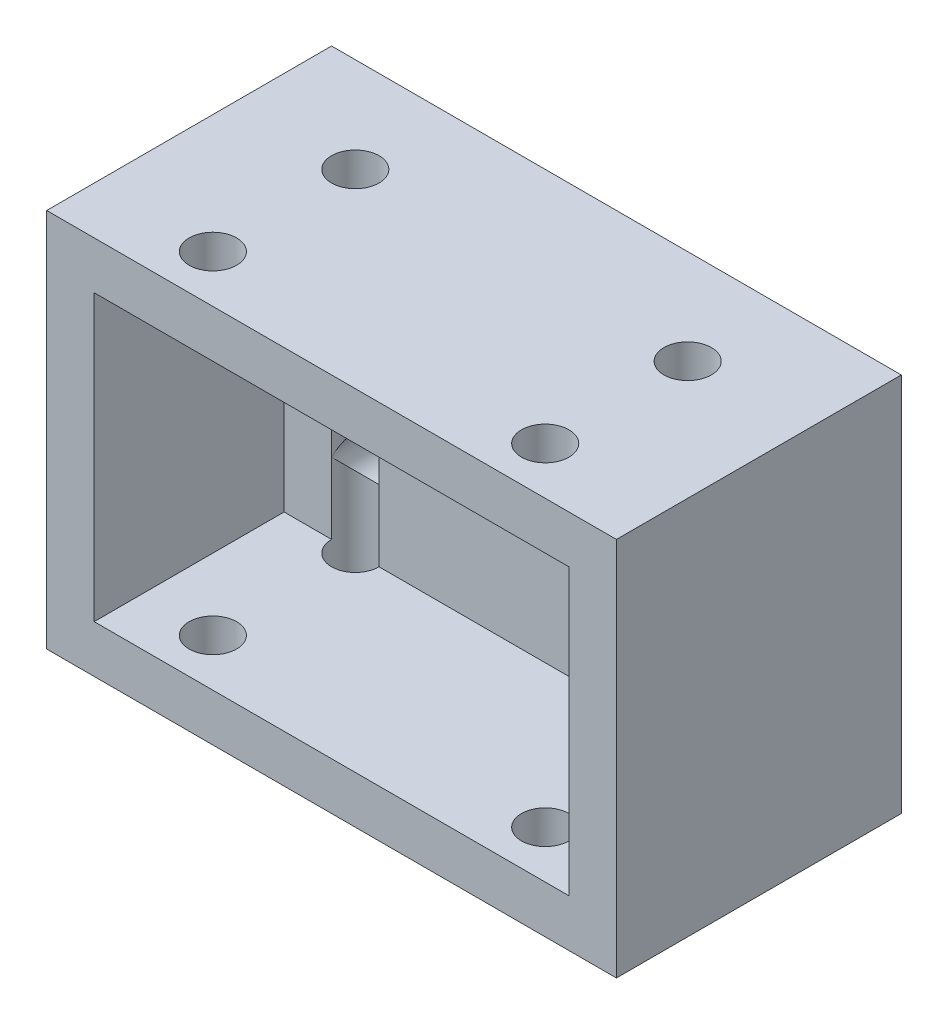
SolidWorks part; units mm, degrees
material "5052-H32"
ref_plane "Front Plane" through (0, 0, 0) normal (0, 0, 1) x (1, 0, 0)
ref_plane "Top Plane" through (0, 0, 0) normal (0, 1, 0) x (1, 0, 0)
ref_plane "Right Plane" through (0, 0, 0) normal (1, 0, 0) x (0, 0, -1)
sketch "Sketch1" plane through (0, 0, 0) normal (0, 0, 1) x (1, 0, 0)
  line L1 (-30, 20) -> (30, 20)
  line L2 (-30, 20) -> (-30, -20)
  line L3 (-30, -20) -> (30, -20)
  line L4 (30, 20) -> (30, -20)
  line L5 (-30, 20) -> (30, -20) construction
  line L6 (-30, -20) -> (30, 20) construction
  circle A0 centre (-17.5, 7.5) radius 2.5
  circle A1 centre (17.5, 7.5) radius 2.5
  circle A2 centre (-17.5, -7.5) radius 2.5
  circle A3 centre (17.5, -7.5) radius 2.5
  point P0 (0, 0)
  dimension "D3" = 5
  dimension "D4" = 5
  dimension "D5" = 5
  dimension "D6" = 5
  dimension "D1" = 60
  dimension "D2" = 40
  dimension "D7" = 12.5
  dimension "D8" = 12.5
  dimension "D9" = 12.5
  dimension "D10" = 12.5
  dimension "D11" = 15
  dimension "D12" = 12.5
  dimension "D13" = 12.5
  dimension "D14" = 15
extrude "Boss-Extrude3" add sketch "Sketch1" along normal blind 30
sketch "Sketch4" plane through (0, 0, 30) normal (0, 0, 1) x (1, 0, 0)
  line L1 (-25, 15) -> (25, 15)
  line L2 (-25, 15) -> (-25, -15)
  line L3 (-25, -15) -> (25, -15)
  line L4 (25, 15) -> (25, -15)
  line L5 (-25, 15) -> (25, -15) construction
  line L6 (-25, -15) -> (25, 15) construction
  point P0 (0, 0)
  dimension "D1" = 50
  dimension "D2" = 30
extrude "Cut-Extrude1" cut sketch "Sketch4" against normal blind 20
sketch "Sketch5" plane through (0, 20, 0) normal (0, 1, 0) x (1, 0, 0)
  line L0 (30, 0) -> (-30, 0) construction
  line L1 (-30, -30) -> (-30, 0) construction
  circle A0 centre (-17.5, -10) radius 2.5
  circle A1 centre (17.5, -10) radius 2.5
  circle A2 centre (17.5, -25) radius 2.5
  circle A3 centre (-17.5, -25) radius 2.5
  point P8 (0, 0)
  point P9 (0, 0)
  point P10 (0, 0)
  point P11 (0, 0)
  dimension "D1" = 5
  dimension "D2" = 35
  dimension "D3" = 15
  dimension "D4" = 10
  dimension "D5" = 12.5
extrude "Cut-Extrude4" cut sketch "Sketch5" against normal blind 49
